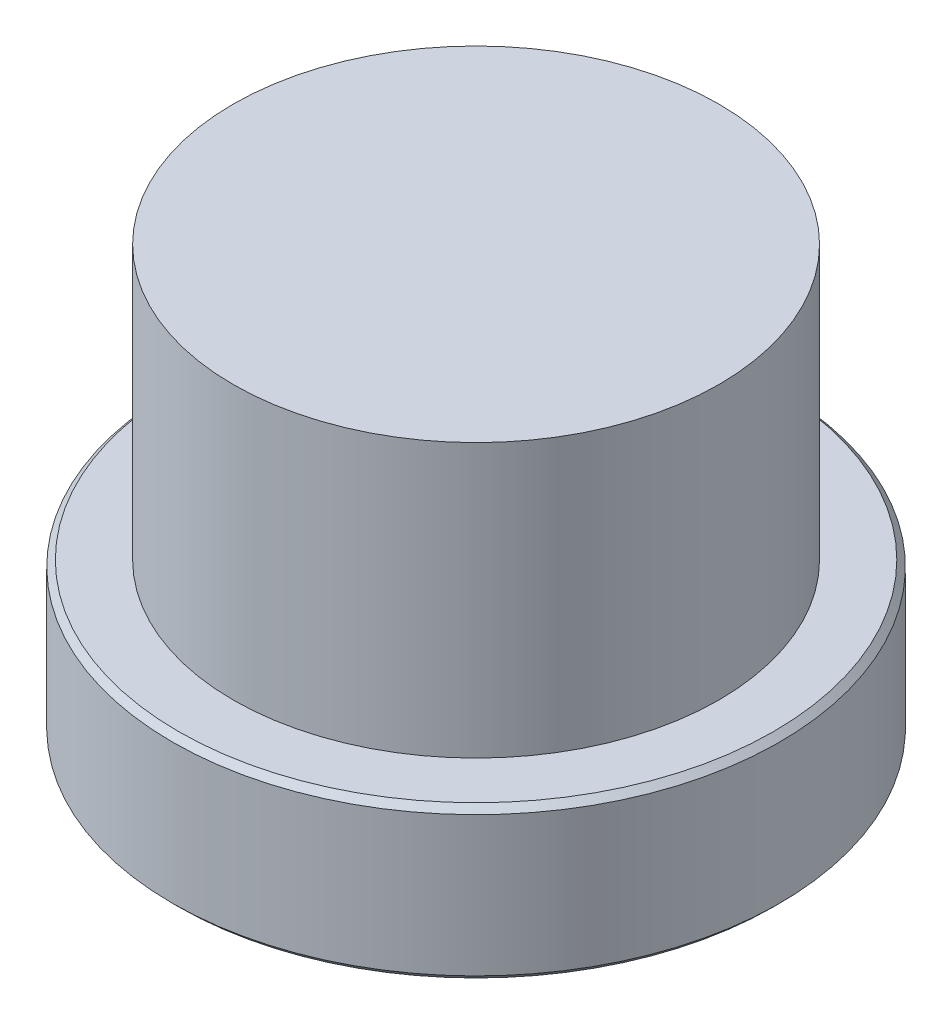
SolidWorks part; units mm, degrees
ref_plane "Plan de face" through (0, 0, 0) normal (0, 0, 1) x (1, 0, 0)
ref_plane "Plan de dessus" through (0, 0, 0) normal (0, 1, 0) x (1, 0, 0)
ref_plane "Plan de droite" through (0, 0, 0) normal (1, 0, 0) x (0, 0, -1)
sketch "Esquisse1" plane through (0, 0, 0) normal (0, 0, 1) x (1, 0, 0)
  line L0 (-98, 25) -> (-100, 23)
  line L1 (-80, 25) -> (-98, 25)
  line L2 (-100, 23) -> (-100, -23)
  line L3 (-98, -25) -> (0, -25)
  line L4 (-100, -23) -> (-98, -25)
  line L5 (0, 25) -> (0, -31.8779) construction
  line L6 (0, -25) -> (0, 115)
  line L8 (-80, 25) -> (-80, 115)
  line L9 (-80, 115) -> (0, 115)
  point P3 (-100, 25)
  point P5 (-100, -25)
revolve "Révolution1" add sketch "Esquisse1" angle 360 about L5
